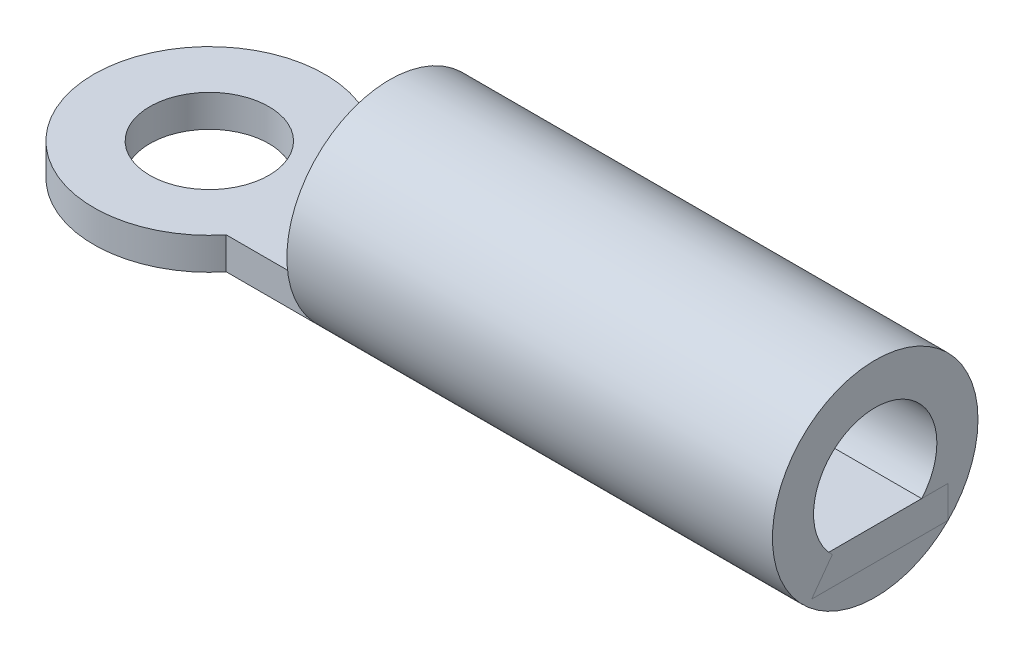
SolidWorks part; units mm, degrees
material "Rostfreier Schmiedestahl"
ref_plane "Ebene vorne" through (0, 0, 0) normal (0, 0, 1) x (1, 0, 0)
ref_plane "Ebene oben" through (0, 0, 0) normal (0, 1, 0) x (1, 0, 0)
ref_plane "Ebene rechts" through (0, 0, 0) normal (1, 0, 0) x (0, 0, -1)
sketch "Skizze1" plane through (0, 0, 0) normal (0, 1, 0) x (1, 0, 0)
  line L0 (2.7717, 2.25) -> (20.57, 2.25)
  line L1 (20.57, -2.25) -> (2.7717, -2.25)
  line L2 (20.57, 2.25) -> (20.57, -2.25)
  line L3 (20.57, 0) -> (0, 0) construction
  circle A0 centre (0, 0) radius 1.84
  arc A1 (2.7717, 2.25) -> (2.7717, -2.25) centre (0, 0) ccw
  dimension "D1" = 3.68
  dimension "D2" = 3.57
  dimension "D3" = 20.57
  dimension "D4" = 4.5
extrude "Aufsatz-Linear austragen1" add sketch "Skizze1" along normal blind 0.99
sketch "Skizze2" plane through (20.57, 0, 0) normal (1, 0, 0) x (0, 0, -1)
  line L0 (0, 0) -> (0, 2.2401) construction
  line L1 (-2.25, 0) -> (2.25, 0) construction
  circle A0 centre (0, 2.2401) radius 3.175
  circle A1 centre (0, 2.2401) radius 1.905
  dimension "D1" = 3.81
  dimension "D2" = 6.35
extrude "Aufsatz-Linear austragen2" add sketch "Skizze2" against normal blind 15 separate body
